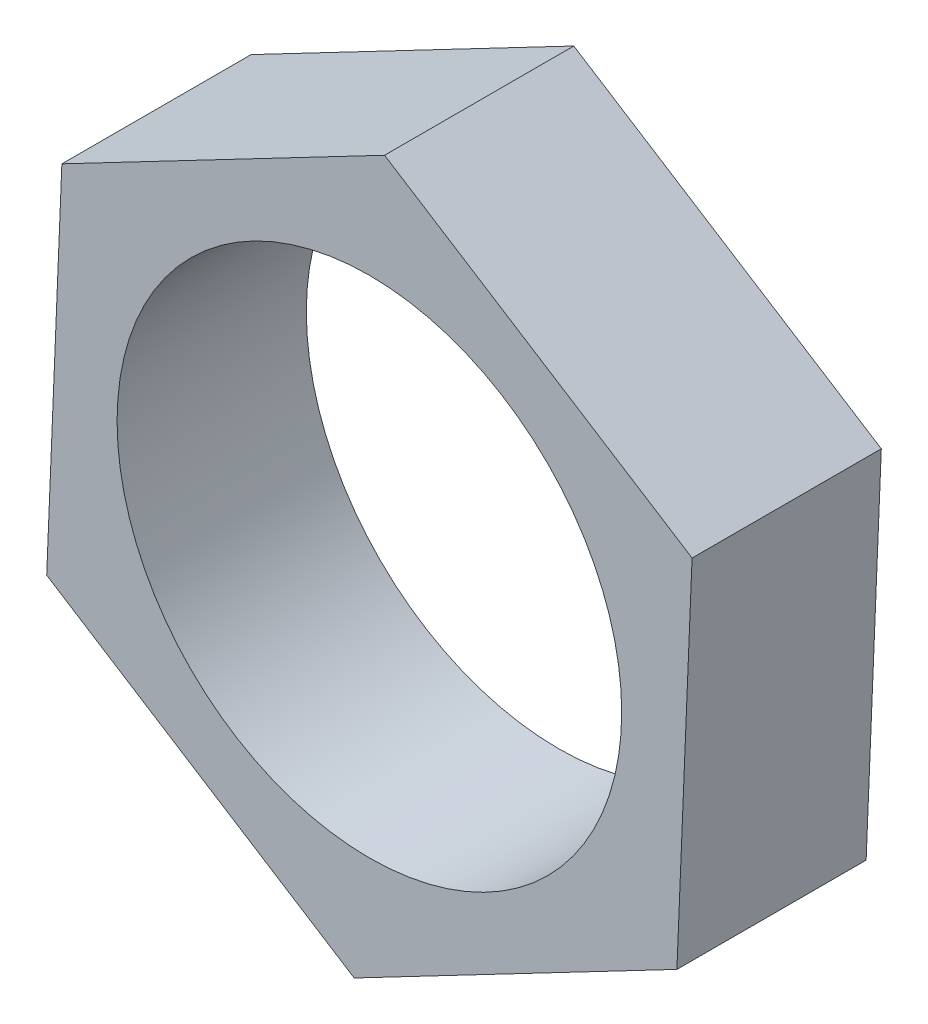
SolidWorks part; units mm, degrees
ref_plane "前视基准面" through (0, 0, 0) normal (0, 0, 1) x (1, 0, 0)
ref_plane "上视基准面" through (0, 0, 0) normal (0, 1, 0) x (1, 0, 0)
ref_plane "右视基准面" through (0, 0, 0) normal (1, 0, 0) x (0, 0, -1)
sketch "草图1" plane through (0, 0, 0) normal (0, 0, 1) x (1, 0, 0)
  line L1 (4.8754, -3.0926) -> (5.1159, 2.6759)
  line L2 (5.1159, 2.6759) -> (0.2406, 5.7685)
  line L3 (0.2406, 5.7685) -> (-4.8754, 3.0926)
  line L4 (-4.8754, 3.0926) -> (-5.1159, -2.6759)
  line L5 (-5.1159, -2.6759) -> (-0.2406, -5.7685)
  line L6 (-0.2406, -5.7685) -> (4.8754, -3.0926)
  circle A0 centre (0, 0) radius 5 construction
  dimension "D1" = 10
extrude "凸台-拉伸1" add sketch "草图1" along normal blind 3
sketch "草图2" plane through (0, 0, 3) normal (0, 0, 1) x (1, 0, 0)
  circle A0 centre (0, 0) radius 4
  dimension "D1" = 8
extrude "切除-拉伸1" cut sketch "草图2" against normal blind 3
